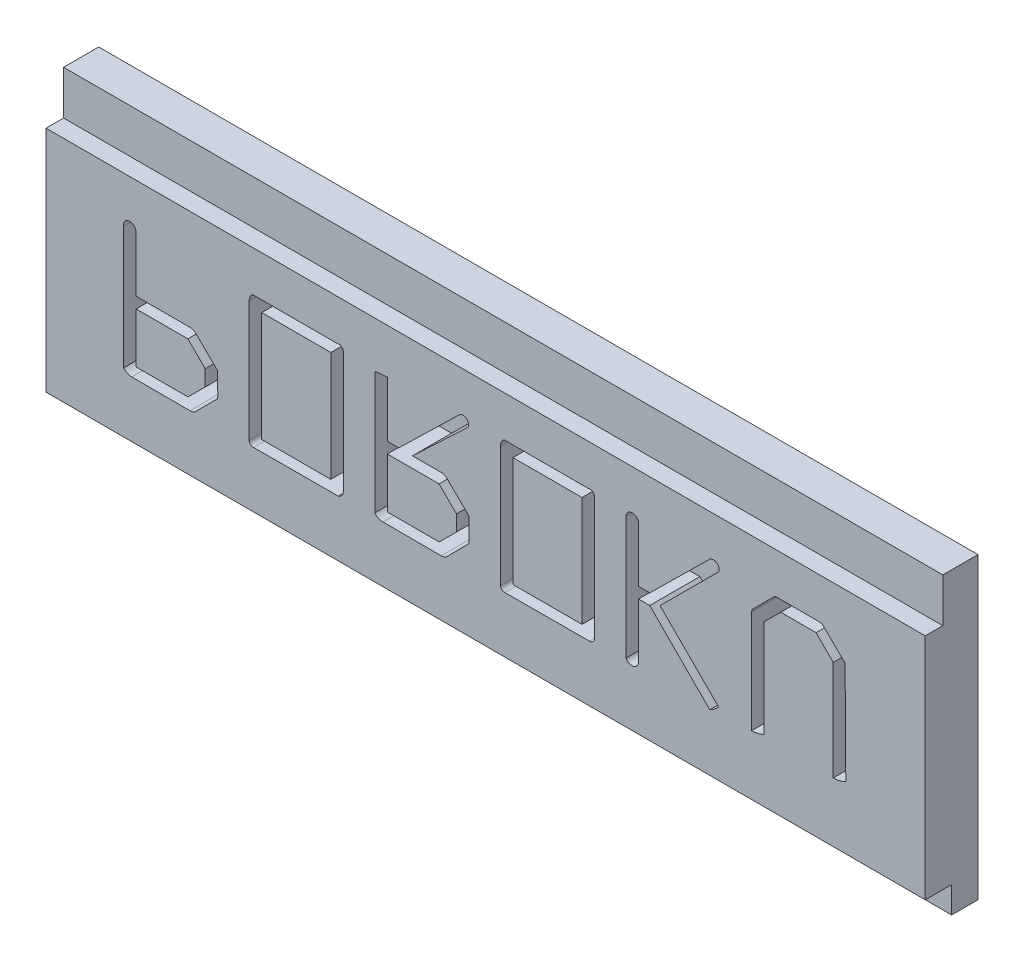
SolidWorks part; units mm, degrees
ref_plane "Front Plane" through (0, 0, 0) normal (0, 0, 1) x (1, 0, 0)
ref_plane "Top Plane" through (0, 0, 0) normal (0, 1, 0) x (1, 0, 0)
ref_plane "Right Plane" through (0, 0, 0) normal (1, 0, 0) x (0, 0, -1)
sketch "Sketch1" plane through (0, 0, 0) normal (0, 1, 0) x (1, 0, 0)
  line L1 (0, 0) -> (100, 0)
  line L2 (0, 0) -> (0, 50)
  line L3 (0, 50) -> (100, 50)
  line L4 (100, 0) -> (100, 50)
  dimension "D1" = 50
  dimension "D2" = 100
extrude "Boss-Extrude1" add sketch "Sketch1" along normal blind 6
sketch "Sketch2" plane through (100, 0, 0) normal (1, 0, 0) x (0, 0, -1)
  line L1 (0, 0) -> (10, 0)
  line L2 (0, 0) -> (0, 3)
  line L3 (0, 3) -> (10, 3)
  line L4 (10, 0) -> (10, 3)
  dimension "D1" = 10
  dimension "D2" = 3
extrude "Cut-Extrude1" cut sketch "Sketch2" against normal through all
sketch "Sketch3" plane through (100, 0, 0) normal (1, 0, 0) x (0, 0, -1)
  line L1 (50, 0) -> (44, 0)
  line L2 (50, 0) -> (50, 34)
  line L3 (50, 34) -> (44, 34)
  line L4 (44, 0) -> (44, 34)
  dimension "D1" = 6
  dimension "D2" = 34
extrude "Boss-Extrude2" add sketch "Sketch3" against normal up to surface (100 mm away) up to face at (0, 3, -20)
sketch "Sketch4" plane through (0, 0, 0) normal (-1, 0, 0) x (0, 0, 1)
  line L1 (-44, 34) -> (-46, 34)
  line L2 (-44, 34) -> (-44, 29)
  line L3 (-44, 29) -> (-46, 29)
  line L4 (-46, 34) -> (-46, 29)
  dimension "D1" = 2
  dimension "D2" = 5
extrude "Cut-Extrude2" cut sketch "Sketch4" against normal through all
sketch "Sketch5" plane through (0, 0, -44) normal (0, 0, -1) x (-1, 0, 0)
  line L0 (-7, 25) -> (-95, 25) construction
  line L1 (-45.0882, 17.5714) -> (-45.4397, 17.4542)
  line L2 (0, 34) -> (-100, 34) construction
  line L5 (-17.0385, 9.6194) -> (-19.4883, 12.0859)
  line L6 (-19.4883, 12.0859) -> (-19.5357, 12.3092)
  line L7 (-19.5357, 12.3092) -> (-19.5273, 14.7589)
  line L8 (-19.5273, 14.7589) -> (-19.4855, 14.904)
  line L9 (-19.4855, 14.904) -> (-16.8962, 17.4542)
  line L10 (-16.8962, 17.4542) -> (-16.5558, 17.5714)
  line L11 (-16.5558, 17.5714) -> (-10.25, 17.5714)
  line L12 (-10.25, 17.5714) -> (-10.2444, 23.8689)
  line L13 (-8.8214, 23.7405) -> (-8.8214, 9.8008)
  line L15 (-9.7478, 9.3767) -> (-16.3744, 9.3571)
  line L16 (-18.1071, 12.5631) -> (-16.154, 10.6071)
  line L17 (-16.154, 10.6071) -> (-10.25, 10.6071)
  line L18 (-10.25, 10.6071) -> (-10.25, 16.3214)
  line L19 (-10.25, 16.3214) -> (-16.1373, 16.3214)
  line L20 (-16.1373, 16.3214) -> (-18.1071, 14.3683)
  line L21 (-18.1071, 14.3683) -> (-18.1071, 12.5631)
  line L23 (-33.8214, 10.1328) -> (-33.8158, 23.88)
  line L25 (-33.1406, 24.3571) -> (-23.5089, 24.3571)
  line L27 (-23.1071, 23.5229) -> (-23.1071, 9.7812)
  line L28 (-23.6094, 9.3571) -> (-33.2355, 9.3795)
  line L29 (-32.3929, 23.1071) -> (-32.3929, 10.6071)
  line L30 (-32.3929, 10.6071) -> (-24.5357, 10.6071)
  line L31 (-24.5357, 10.6071) -> (-24.5357, 23.1071)
  line L32 (-24.5357, 23.1071) -> (-32.3929, 23.1071)
  line L33 (-45.6099, 9.6194) -> (-48.0597, 12.0859)
  line L34 (-48.0597, 12.0859) -> (-48.1071, 12.3092)
  line L35 (-48.1071, 12.3092) -> (-48.0988, 14.7617)
  line L36 (-48.0988, 14.7617) -> (-48.0569, 14.9012)
  line L37 (-48.0569, 14.9012) -> (-45.4397, 17.4542)
  line L39 (-45.0882, 17.5714) -> (-41.6814, 17.5714)
  line L40 (-41.6814, 17.5714) -> (-48.0318, 23.5731)
  line L41 (-46.9911, 24.2595) -> (-40.1161, 17.5714)
  line L42 (-40.1161, 17.5714) -> (-38.8214, 17.5714)
  line L43 (-38.8214, 17.5714) -> (-38.8186, 23.88)
  line L44 (-37.3929, 23.7405) -> (-37.3929, 9.8008)
  line L46 (-38.3192, 9.3767) -> (-44.9459, 9.3571)
  line L47 (-46.6786, 12.5575) -> (-44.7254, 10.6071)
  line L48 (-44.7254, 10.6071) -> (-38.8214, 10.6071)
  line L49 (-38.8214, 10.6071) -> (-38.8214, 16.3214)
  line L50 (-38.8214, 16.3214) -> (-44.7087, 16.3214)
  line L51 (-44.7087, 16.3214) -> (-46.6786, 14.3544)
  line L52 (-46.6786, 14.3544) -> (-46.6786, 12.5575)
  line L54 (-62.3929, 10.1328) -> (-62.3873, 23.88)
  line L56 (-61.7121, 24.3571) -> (-52.0804, 24.3571)
  line L58 (-51.6786, 23.5229) -> (-51.6786, 9.7812)
  line L59 (-52.1808, 9.3571) -> (-61.8069, 9.3795)
  line L60 (-60.9643, 23.1071) -> (-60.9643, 10.6071)
  line L61 (-60.9643, 10.6071) -> (-53.1071, 10.6071)
  line L62 (-53.1071, 10.6071) -> (-53.1071, 23.1071)
  line L63 (-53.1071, 23.1071) -> (-60.9643, 23.1071)
  line L65 (-76.5167, 10.2249) -> (-69.8343, 16.8906)
  line L66 (-69.8343, 16.8906) -> (-76.5084, 23.5647)
  line L67 (-75.4565, 24.2595) -> (-68.6708, 17.5714)
  line L68 (-68.6708, 17.5714) -> (-67.3929, 17.5714)
  line L69 (-67.3929, 17.5714) -> (-67.3901, 23.88)
  line L70 (-65.9643, 23.7405) -> (-65.9643, 9.7896)
  line L71 (-67.3929, 10.1384) -> (-67.3929, 16.3214)
  line L72 (-67.3929, 16.3214) -> (-68.668, 16.3214)
  line L73 (-68.668, 16.3214) -> (-75.49, 9.466)
  line L74 (-81.6786, 10.13) -> (-81.6786, 21.2266)
  line L75 (-81.6786, 21.2266) -> (-83.5703, 23.1071)
  line L76 (-83.5703, 23.1071) -> (-87.5854, 23.1071)
  line L77 (-87.5854, 23.1071) -> (-89.5357, 21.1512)
  line L78 (-89.5357, 21.1512) -> (-89.5357, 9.7701)
  line L79 (-90.9643, 10.1356) -> (-90.8834, 21.7511)
  line L80 (-90.8834, 21.7511) -> (-88.2578, 24.3209)
  line L81 (-88.2578, 24.3209) -> (-87.8728, 24.3571)
  line L82 (-87.8728, 24.3571) -> (-82.9704, 24.3571)
  line L83 (-82.9704, 24.3571) -> (-82.7891, 24.2344)
  line L84 (-82.7891, 24.2344) -> (-80.303, 21.7427)
  line L85 (-80.303, 21.7427) -> (-80.25, 21.4805)
  line L86 (-80.25, 21.4805) -> (-80.25, 9.7812)
  arc A0 (-10.2444, 23.8689) -> (-8.8214, 23.7405) centre (-9.5272, 23.8682) cw
  arc A1 (-23.6094, 9.3571) -> (-23.1071, 9.7812) centre (-23.6082, 9.8652) ccw
  arc A2 (-33.8214, 10.1328) -> (-33.2355, 9.3795) centre (-33.0446, 10.1325) ccw
  arc A3 (-33.8158, 23.88) -> (-33.1406, 24.3571) centre (-33.3095, 23.8798) cw
  arc A4 (-23.1071, 23.5229) -> (-23.5089, 24.3571) centre (-24.1742, 23.5229) ccw
  arc A5 (-9.7478, 9.3767) -> (-8.8214, 9.8008) centre (-9.7514, 10.6083) ccw
  arc A6 (-16.3744, 9.3571) -> (-17.0385, 9.6194) centre (-16.3773, 10.3218) cw
  arc A7 (-38.3192, 9.3767) -> (-37.3929, 9.8008) centre (-38.3228, 10.6083) ccw
  arc A8 (-44.9459, 9.3571) -> (-45.6099, 9.6194) centre (-44.9487, 10.3218) cw
  arc A9 (-38.8186, 23.88) -> (-37.3929, 23.7405) centre (-38.8219, 16.4911) cw
  arc A10 (-46.9911, 24.2595) -> (-48.0318, 23.5731) centre (-47.4361, 23.802) ccw
  arc A11 (-52.1808, 9.3571) -> (-51.6786, 9.7812) centre (-52.1796, 9.8652) ccw
  arc A12 (-61.8069, 9.3795) -> (-62.3929, 10.1328) centre (-61.8055, 9.9851) cw
  arc A13 (-62.3873, 23.88) -> (-61.7121, 24.3571) centre (-61.881, 23.8798) cw
  arc A14 (-51.6786, 23.5229) -> (-52.0804, 24.3571) centre (-52.7456, 23.5229) ccw
  arc A15 (-67.3929, 10.1384) -> (-65.9643, 9.7896) centre (-66.636, 10.1384) ccw
  arc A16 (-76.5167, 10.2249) -> (-75.49, 9.466) centre (-73.495, 13.239) ccw
  arc A17 (-65.9643, 23.7405) -> (-67.3901, 23.88) centre (-66.684, 23.7405) ccw
  arc A18 (-75.4565, 24.2595) -> (-76.5084, 23.5647) centre (-75.9088, 23.8006) ccw
  arc A19 (-80.25, 9.7812) -> (-81.6786, 10.13) centre (-80.25, 12.8814) cw
  arc A20 (-89.5357, 9.7701) -> (-90.9643, 10.1356) centre (-89.5357, 12.7446) cw
  dimension "D1" = 9
extrude "Cut-Extrude3" cut sketch "Sketch5" along normal blind 5.7
sketch "Sketch8" plane through (0, 6, 0) normal (0, 1, 0) x (1, 0, 0)
  line L0 (46.515, 10) -> (46.515, 44) construction
  line L1 (60.1307, 150.748) -> (217.464, 150.748) construction
  line L2 (130, 309) -> (530, 309) construction
  line L3 (101.6667, 132) -> (448.3333, 132) construction
  line L4 (92.1667, 73.5) -> (454.8333, 73.5) construction
  line L12 (92.1667, 73.5) -> (454.8333, 73.5) construction
  line L30 (100, 44) -> (0, 44) construction
  line L64 (50, 44) -> (50, 5.4119) construction
  line L65 (7.0116, 30.0772) -> (8.9551, 27.3326)
  line L66 (8.4762, 31.0134) -> (10.3204, 28.5061)
  line L67 (10.8168, 31.4007) -> (10.155, 32.7243)
  line L68 (9.8241, 30.4081) -> (10.8168, 31.4007)
  line L69 (9.1624, 31.2353) -> (9.8241, 30.4081)
  line L70 (9.3278, 32.3934) -> (9.1624, 31.2353)
  line L71 (10.155, 32.7243) -> (9.3278, 32.3934)
  line L72 (12.8021, 32.2279) -> (11.644, 33.7169)
  line L73 (11.644, 31.7316) -> (12.8021, 32.2279)
  line L74 (11.644, 31.7316) -> (11.0923, 32.5507)
  line L75 (13.193, 29.9735) -> (13.8548, 28.8154)
  line L76 (13.8548, 28.8154) -> (8.5607, 26.3338)
  line L77 (8.5607, 26.3338) -> (7.4026, 26.8301)
  line L78 (7.4026, 26.8301) -> (9.057, 19.8816)
  line L79 (9.057, 19.8816) -> (13.6893, 20.0471)
  line L80 (15.8401, 28.65) -> (13.8548, 31.6279)
  line L81 (13.8548, 31.6279) -> (10.7114, 30.139)
  line L82 (10.7114, 30.139) -> (12.3658, 29.4772)
  line L83 (13.193, 29.9735) -> (12.3658, 29.4772)
  line L84 (31.2401, 25.85) -> (31.2401, 28.65)
  line L85 (28.4401, 25.85) -> (31.2401, 25.85)
  line L86 (28.4401, 23.05) -> (28.4401, 25.85)
  line L87 (25.6401, 23.05) -> (28.4401, 23.05)
  line L88 (25.6401, 25.85) -> (25.6401, 23.05)
  line L89 (22.8401, 25.85) -> (25.6401, 25.85)
  line L90 (22.8401, 28.65) -> (22.8401, 25.85)
  line L91 (25.6401, 28.65) -> (22.8401, 28.65)
  line L92 (25.6401, 31.45) -> (25.6401, 28.65)
  line L93 (28.4401, 31.45) -> (25.6401, 31.45)
  line L94 (28.4401, 28.65) -> (28.4401, 31.45)
  line L95 (31.2401, 28.65) -> (28.4401, 28.65)
  line L96 (52.0414, 30.75) -> (42.5414, 30.75)
  line L97 (52.0414, 30.75) -> (52.0414, 23.75)
  line L98 (52.0414, 23.75) -> (42.5414, 23.75)
  line L99 (42.5414, 20.75) -> (42.5414, 23.75)
  line L100 (37.9901, 27.25) -> (42.5414, 20.75)
  line L101 (42.5414, 33.75) -> (37.9901, 27.25)
  line L102 (42.5414, 30.75) -> (42.5414, 33.75)
  line L103 (60.4193, 21.3393) -> (59.0414, 29.1538)
  line L104 (68.2338, 19.9614) -> (60.4193, 21.3393)
  line L105 (66.1125, 22.0827) -> (68.2338, 19.9614)
  line L106 (72.83, 28.8003) -> (66.1125, 22.0827)
  line L107 (67.8803, 33.75) -> (72.83, 28.8003)
  line L108 (61.1627, 27.0325) -> (67.8803, 33.75)
  line L109 (59.0414, 29.1538) -> (61.1627, 27.0325)
  line L110 (90.03, 33.75) -> (90.03, 24.25)
  line L111 (90.03, 33.75) -> (83.03, 33.75)
  line L112 (83.03, 33.75) -> (83.03, 24.25)
  line L113 (80.03, 24.25) -> (83.03, 24.25)
  line L114 (86.4768, 19.6614) -> (80.03, 24.25)
  line L115 (93.03, 24.25) -> (86.4768, 19.6614)
  line L116 (90.03, 24.25) -> (93.03, 24.25)
  spline S9 degree 2 poles (7.8995, 26.9338) (6.9675, 27.996) (6.1739, 29.1623) knots 0 0 0 1 1 1
  spline S10 degree 3 poles (8.9551, 27.3326) (9.1296, 26.7307) (8.2077, 26.5734) (7.8995, 26.9338) knots 0 0 0 0 1 1 1 1
  spline S11 degree 3 poles (6.1739, 29.1623) (5.8271, 29.6649) (6.5306, 30.2426) (7.0116, 30.0772) knots 0 0 0 0 1 1 1 1
  spline S12 degree 3 poles (7.5484, 30.4081) (7.4209, 30.7808) (7.6573, 31.5729) (8.1697, 31.4007) knots 0 0 0 0 1 1 1 1
  spline S13 degree 2 poles (7.5484, 30.4081) (8.3692, 29.0037) (9.4644, 27.8067) knots 0 0 0 1 1 1
  spline S14 degree 3 poles (10.3204, 28.5061) (10.7529, 28.0224) (9.8445, 27.3259) (9.4644, 27.8067) knots 0 0 0 0 1 1 1 1
  spline S15 degree 2 poles (8.1697, 31.4007) (8.3652, 31.2409) (8.4762, 31.0134) knots 0 0 0 1 1 1
  spline S16 degree 2 poles (11.644, 33.7169) (10.8014, 33.411) (11.0923, 32.5507) knots 0 0 0 1 1 1
  spline S17 degree 3 poles (13.6893, 20.0471) (12.4502, 27.1719) (13.7772, 23.8367) (15.8401, 28.65) knots 0 0 0 0 1 1 1 1
extrude "Cut-Extrude4" cut sketch "Sketch8" against normal blind 5.5
sketch "Sketch9" plane through (0, 0, 0) normal (-1, 0, 0) x (0, 0, 1)
  line L0 (-50, 0) -> (-10, 0) construction
  line L1 (0, 6) -> (-44, 6)
  line L2 (0, 6) -> (0, 0)
  line L3 (0, 0) -> (-44, 0)
  line L4 (-44, 6) -> (-44, 3)
  line L5 (-44, 0) -> (-47, 0)
  line L6 (-47, 0) -> (-47, 3)
  line L7 (-47, 3) -> (-44, 3)
  line L8 (-44, 6) -> (-44, 29) construction
  line L10 (-50, 34) -> (-50, 0) construction
  dimension "D1" = 3
  dimension "D2" = 3
  dimension "D3" = 3
extrude "Cut-Extrude5" cut sketch "Sketch9" against normal through all
